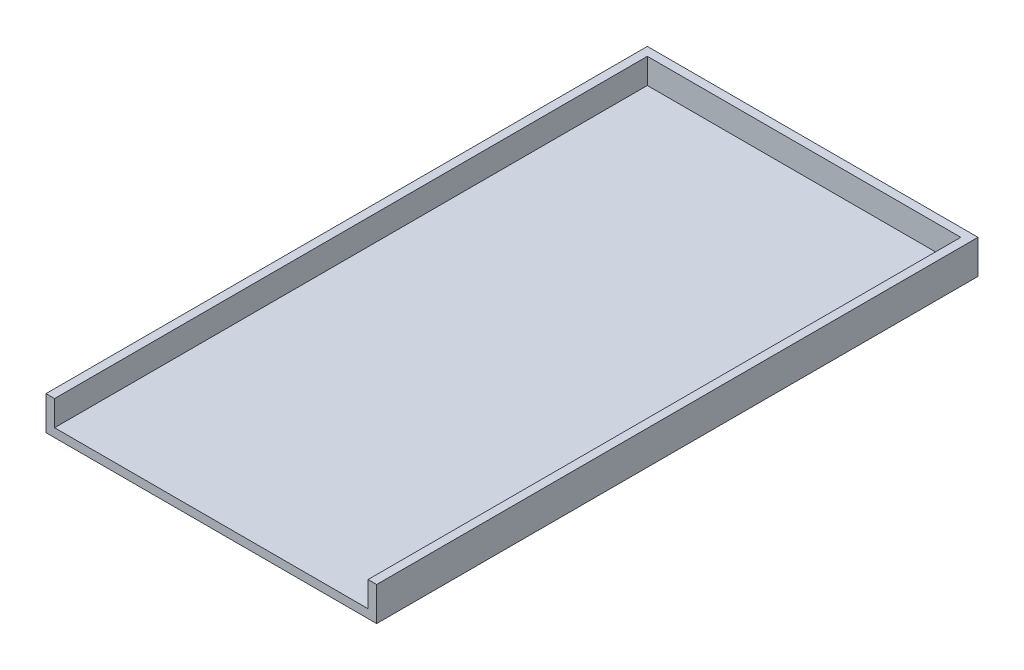
SolidWorks part; units mm, degrees
ref_plane "Front Plane" through (0, 0, 0) normal (0, 0, 1) x (1, 0, 0)
ref_plane "Top Plane" through (0, 0, 0) normal (0, 1, 0) x (1, 0, 0)
ref_plane "Right Plane" through (0, 0, 0) normal (1, 0, 0) x (0, 0, -1)
sketch "Sketch2" plane through (0, 0, 0) normal (0, 0, 1) x (1, 0, 0)
  line L0 (36.9535, -65.9138) -> (36.9535, -53.3932)
  line L7 (36.9535, -53.3932) -> (-85.2483, -53.3932)
  line L8 (-85.2483, -65.9138) -> (-85.2483, -53.3932)
  line L9 (36.9535, -65.9138) -> (-85.2483, -65.9138)
  point P0 (0, 0)
  point P1 (0, 0)
  point P2 (-83.8126, -65.0227)
  point P3 (-85.2483, -65.9138)
  point P4 (36.9535, -53.3932)
extrude "Boss-Extrude1" add sketch "Sketch2" along normal blind 222.25
shell "Shell1" thickness 3.175
